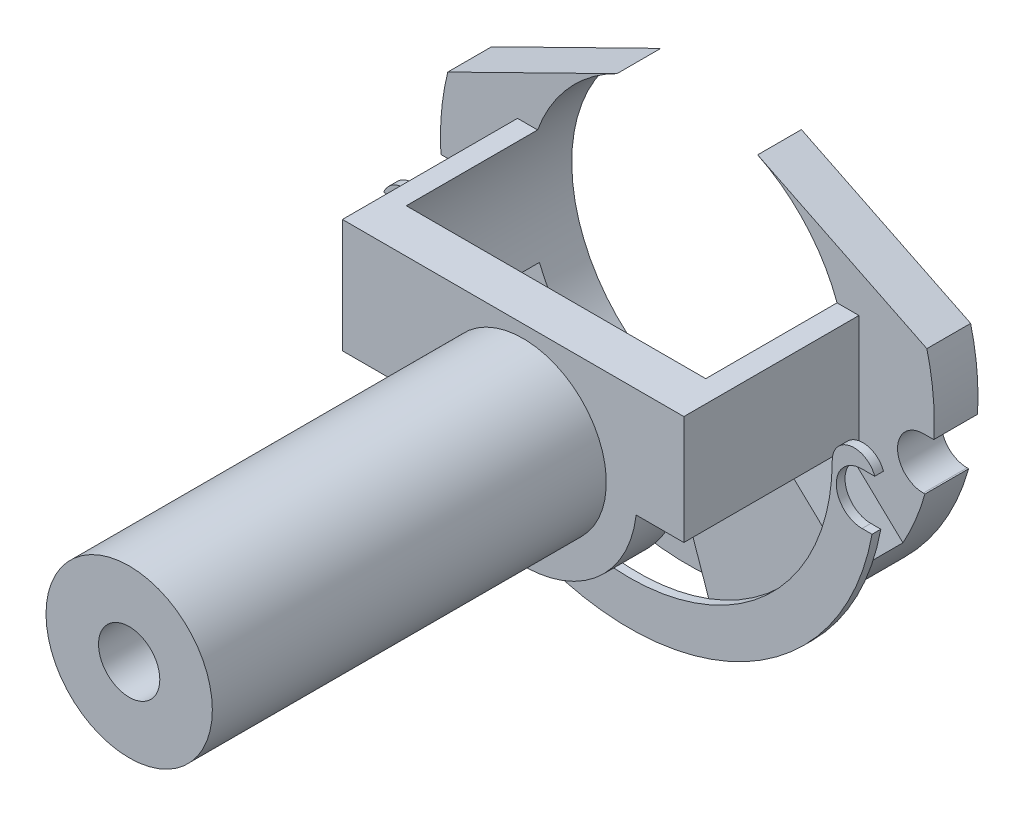
SolidWorks part; units mm, degrees
ref_plane "Alzado" through (0, 0, 0) normal (0, 0, 1) x (1, 0, 0)
ref_plane "Planta" through (0, 0, 0) normal (0, 1, 0) x (1, 0, 0)
ref_plane "Vista lateral" through (0, 0, 0) normal (1, 0, 0) x (0, 0, -1)
sketch "Croquis1" plane through (0, 0, 0) normal (0, 0, 1) x (1, 0, 0)
  circle A0 centre (0, 0) radius 9.5
extrude "Saliente-Extruir1" add sketch "Croquis1" along normal blind 45
sketch "Croquis2" plane through (0, 0, 0) normal (0, 0, -1) x (-1, 0, 0)
  line L0 (-13.8603, 10.9499) -> (16.1397, 10.9499)
  line L1 (-13.8603, 10.9499) -> (-15.8603, 10.9499)
  line L2 (-15.8603, 10.9499) -> (-15.8603, -1.5097)
  line L3 (-15.8603, -1.5097) -> (-12.912, -1.5097)
  line L4 (16.1397, 10.9499) -> (18.1397, 10.9499)
  line L5 (18.1397, 10.9499) -> (18.1397, -2.0501)
  line L6 (18.1397, -2.0501) -> (12.8373, -2.0501)
  arc A0 (-12.912, -1.5097) -> (12.8373, -2.0501) centre (0, 0) ccw
extrude "Saliente-Extruir2" add sketch "Croquis2" along normal blind 5
ref_plane "Plano1" through (0, 0, 0) normal (0, 0, 1) x (1, 0, 0)
sketch "Croquis3" plane through (0, 0, 0) normal (0, 0, 1) x (1, 0, 0)
  line L0 (15.8603, 10.9499) -> (18.3603, 10.9499)
  line L1 (18.3603, 10.9499) -> (18.3603, -1.5097)
  line L2 (18.3603, -1.5097) -> (15.8603, -1.5097)
  line L3 (15.8603, -1.5097) -> (15.8603, 10.9499)
  line L4 (-18.1397, 10.9499) -> (15.8603, 10.9499) construction
  line L5 (15.8603, -1.5097) -> (12.912, -1.5097) construction
  line L6 (-18.1397, 10.9499) -> (-18.1397, -2.0501)
  line L7 (-18.1397, -2.0501) -> (-20.6397, -2.0501)
  line L8 (-20.6397, -2.0501) -> (-20.6397, 10.9499)
  line L9 (-20.6397, 10.9499) -> (-18.1397, 10.9499)
extrude "Saliente-Extruir3" add sketch "Croquis3" against normal blind 20
ref_plane "Plano2" through (0, 0, -20) normal (0, 0, -1) x (-1, 0, 0)
sketch "Croquis4" plane through (0, 0, -20) normal (0, 0, -1) x (-1, 0, 0)
  line L0 (-26.1202, 11.5491) -> (-6.789, 21.0547)
  line L2 (28.6063, 11.5491) -> (9.2751, 21.0547)
  arc A0 (-6.789, 21.0547) -> (9.2751, 21.0547) centre (1.243, 4.7201) ccw
  arc A1 (-26.1202, 11.5491) -> (28.6063, 11.5491) centre (1.243, 4.7201) ccw
  circle A2 centre (1.243, 4.7201) radius 18.2026 construction
  circle A3 centre (1.243, 4.7201) radius 28.2026 construction
extrude "Saliente-Extruir4" add sketch "Croquis4" along normal blind 5
sketch "Croquis5" plane through (0, 0, -20) normal (0, 0, -1) x (-1, 0, 0)
  line L0 (-15.8603, 10.9499) -> (-15.8603, -1.5097) construction
  line L1 (-15.8603, 10.9499) -> (-15.8603, -1.5097)
  arc A0 (-15.8603, 10.9499) -> (-15.8603, -1.5097) centre (1.243, 4.7201) ccw construction
  arc A1 (-15.8603, 10.9499) -> (-15.8603, -1.5097) centre (1.243, 4.7201) ccw
extrude "Cortar-Extruir1" cut sketch "Croquis5" against normal up to surface (15 mm away) up to face at (-2.8539, 0.5488, -5)
sketch "Croquis6" plane through (0, 0, -20) normal (0, 0, -1) x (-1, 0, 0)
  line L0 (18.1397, -2.0501) -> (18.1397, 10.9499) construction
  line L1 (18.1397, 10.9499) -> (18.3464, 10.9499) construction
  line L2 (18.1397, -2.0501) -> (18.1397, 10.9499)
  line L3 (18.1397, 10.9499) -> (18.3464, 10.9499)
  arc A0 (18.1397, -2.0501) -> (18.3464, 10.9499) centre (1.243, 4.7201) ccw construction
  arc A1 (18.1397, -2.0501) -> (18.3464, 10.9499) centre (1.243, 4.7201) ccw
extrude "Cortar-Extruir2" cut sketch "Croquis6" against normal up to surface (15 mm away) up to face at (-2.8539, -1.5278, -5)
sketch "Croquis8" plane through (0, 0, -20) normal (0, 0, 1) x (1, 0, 0)
  line L0 (23.3805, -9.03) -> (15.7541, -1.7938)
  line L1 (7.9934, -21.9271) -> (4.7184, -12.4786)
  arc A0 (-18.1397, -2.0501) -> (15.8603, -1.5097) centre (-1.243, 4.7201) ccw construction
  arc A1 (-28.6063, 11.5491) -> (26.1202, 11.5491) centre (-1.243, 4.7201) ccw construction
  arc A2 (4.7184, -12.4786) -> (15.7541, -1.7938) centre (-1.243, 4.7201) ccw
  arc A3 (7.9934, -21.9271) -> (23.3805, -9.03) centre (-1.243, 4.7201) ccw
extrude "Saliente-Extruir6" add sketch "Croquis8" along normal blind 6
ref_plane "Plano3" through (0, 0, -14) normal (0, 0, 1) x (1, 0, 0)
ref_plane "Plano4" through (-28.6063, 11.5491, -20) normal (0.2421, 0.9702, 0) x (0.9702, -0.2421, 0)
sketch "Croquis10" plane through (0, 0, -14) normal (0, 0, 1) x (1, 0, 0)
  arc A0 (-29.0944, 2.0964) -> (27.3107, 2.0964) centre (-0.8919, 2.0964) ccw
  arc A5 (27.3107, 2.0964) -> (22.3107, 2.0964) centre (24.8107, 2.0964) ccw
  arc A9 (-24.0944, 2.0964) -> (-29.0944, 2.0964) centre (-26.5944, 2.0964) ccw
  arc A10 (-24.0944, 2.0964) -> (22.3107, 2.0964) centre (-0.8919, 2.0964) ccw
extrude "Saliente-Extruir9" add sketch "Croquis10" along normal blind 1
sketch "Croquis12" plane through (0, 0, -13) normal (0, 0, 1) x (1, 0, 0)
  line L0 (-27.5639, 3) -> (-28.9254, 3)
  line L1 (-27.5639, -3) -> (-28.6302, -3)
  line L2 (-28.9254, 3) -> (-33.5843, 3)
  line L3 (-33.5843, 3) -> (-33.5843, -3)
  line L4 (-33.5843, -3) -> (-28.6302, -3)
  arc A0 (-27.5639, -3) -> (-27.5639, 3) centre (-27.5639, 0) ccw
  arc A1 (-24.0944, 2.0964) -> (-29.0944, 2.0964) centre (-26.5944, 2.0964) ccw construction
  arc A2 (-29.0944, 2.0964) -> (27.3107, 2.0964) centre (-0.8919, 2.0964) ccw construction
extrude "Cortar-Extruir3" cut sketch "Croquis12" against normal blind 30
sketch "Croquis13" plane through (0, 0, -13) normal (0, 0, 1) x (1, 0, 0)
  line L0 (25.715, 2.9432) -> (33.8546, 2.9432)
  line L1 (33.8546, 2.9432) -> (33.8546, -2.9432)
  line L2 (33.8546, -2.9432) -> (25.715, -2.9432)
  arc A0 (25.715, 2.9432) -> (25.715, -2.9432) centre (25.715, 0) ccw
extrude "Cortar-Extruir4" cut sketch "Croquis13" against normal blind 30
sketch "Croquis14" plane through (0, 0, 45) normal (0, 0, 1) x (1, 0, 0)
  circle A0 centre (0, 0) radius 3.5
  circle A1 centre (0, 0) radius 9.5 construction
extrude "Cortar-Extruir5" cut sketch "Croquis14" against normal through all
